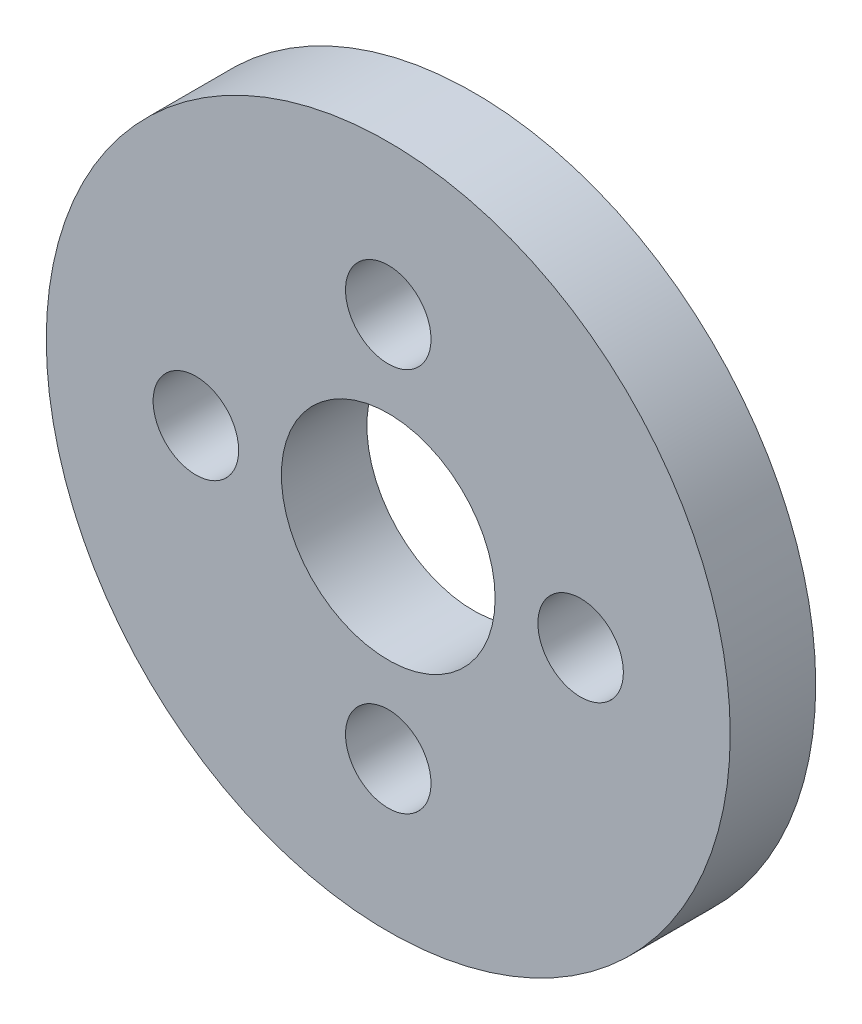
SolidWorks part; units mm, degrees
material "Pine"
ref_plane "Front Plane" through (0, 0, 0) normal (0, 0, 1) x (1, 0, 0)
ref_plane "Top Plane" through (0, 0, 0) normal (0, 1, 0) x (1, 0, 0)
ref_plane "Right Plane" through (0, 0, 0) normal (1, 0, 0) x (0, 0, -1)
sketch "Sketch1" plane through (0, 0, 0) normal (0, 0, 1) x (1, 0, 0)
  circle A0 centre (0, 228.6) radius 7.9375
  circle A1 centre (0, 228.6) radius 25.4
  circle A2 centre (0, 242.8875) radius 3.175 construction
  circle A3 centre (0, 242.8875) radius 3.175
  circle A4 centre (14.2875, 228.6) radius 3.175
  circle A5 centre (0, 214.3125) radius 3.175
  circle A6 centre (-14.2875, 228.6) radius 3.175
  circle A7 centre (0, 228.6) radius 7.9375 construction
  point P18 (0, 228.6)
  dimension "D2" = 50.8
  dimension "D3" = 6.35
  dimension "D5" = 15.875
  dimension "D4" = 4
extrude "Boss-Extrude1" add sketch "Sketch1" along normal blind 6.35
